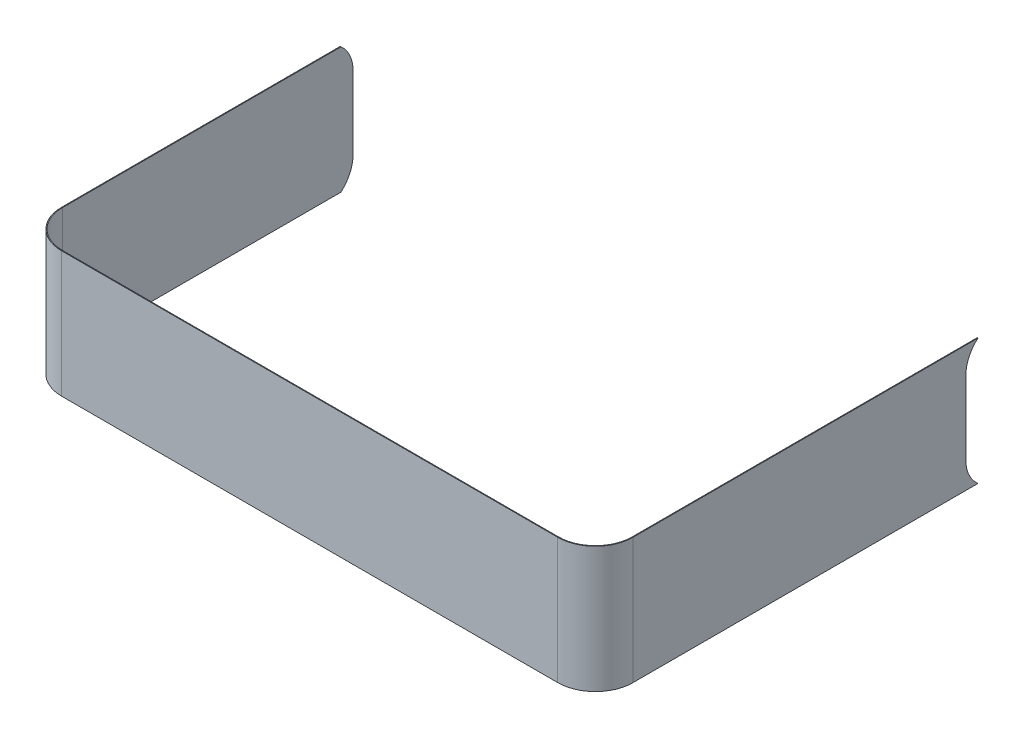
SolidWorks part; units mm, degrees
ref_plane "Front Plane" through (0, 0, 0) normal (0, 0, 1) x (1, 0, 0)
ref_plane "Top Plane" through (0, 0, 0) normal (0, 1, 0) x (1, 0, 0)
ref_plane "Right Plane" through (0, 0, 0) normal (1, 0, 0) x (0, 0, -1)
sketch "Sketch2" plane through (0, 0, 0) normal (0, 1, 0) x (1, 0, 0)
  line L0 (0, 0) -> (6590, 0)
  line L1 (-500, 500) -> (-500, 8890)
  line L2 (7090, 500) -> (7090, 8890)
  line L3 (-500, 8890) -> (-490, 8890)
  line L4 (-490, 8890) -> (-490, 500)
  line L5 (0, 10) -> (6590, 10)
  line L6 (7080, 500) -> (7080, 8890)
  line L7 (7080, 8890) -> (7090, 8890)
  arc A0 (0, 0) -> (-500, 500) centre (0, 500) cw
  arc A1 (6590, 0) -> (7090, 500) centre (6590, 500) ccw
  arc A2 (-490, 500) -> (0, 10) centre (0, 500) ccw
  arc A3 (6590, 10) -> (7080, 500) centre (6590, 500) ccw
extrude "Boss-Extrude2" add sketch "Sketch2" against normal blind 1672 contours L1 L3 L4 A2 L5 A3 L6 L7 L2 A1 L0 A0
sketch "Sketch3" plane through (-500, 0, 0) normal (-1, 0, 0) x (0, 0, 1)
  line L0 (-4822, 110) -> (-3902, 110)
  line L1 (-4002.212, -1770.9516) -> (-4822, -1782)
  line L2 (-4362, -350) -> (-4362, -1322)
  line L3 (-4822, 110) -> (-9056.8826, 110)
  line L4 (-9056.8826, 110) -> (-9056.8826, -1782)
  line L5 (-9056.8826, -1782) -> (-4822, -1782)
  arc A2 (-4362, -350) -> (-3902, 110) centre (-3902, -350) cw
  arc A3 (-4362, -1322) -> (-4002.212, -1770.9516) centre (-3902, -1322) ccw
extrude "Cut-Extrude2" cut sketch "Sketch3" against normal blind 20
sketch "Sketch4" plane through (7090, 0, 0) normal (1, 0, 0) x (0, 0, -1)
  line L0 (5380, 110) -> (9554.6697, 110)
  line L2 (4920, -350) -> (4920, -1322)
  line L3 (9554.6697, 110) -> (9554.6697, -1782)
  line L4 (9554.6697, -1782) -> (5380, -1782)
  arc A0 (4920, -1322) -> (5380, -1782) centre (5380, -1322) ccw
  arc A1 (4920, -350) -> (5380, 110) centre (5380, -350) cw
extrude "Cut-Extrude3" cut sketch "Sketch4" against normal blind 20
